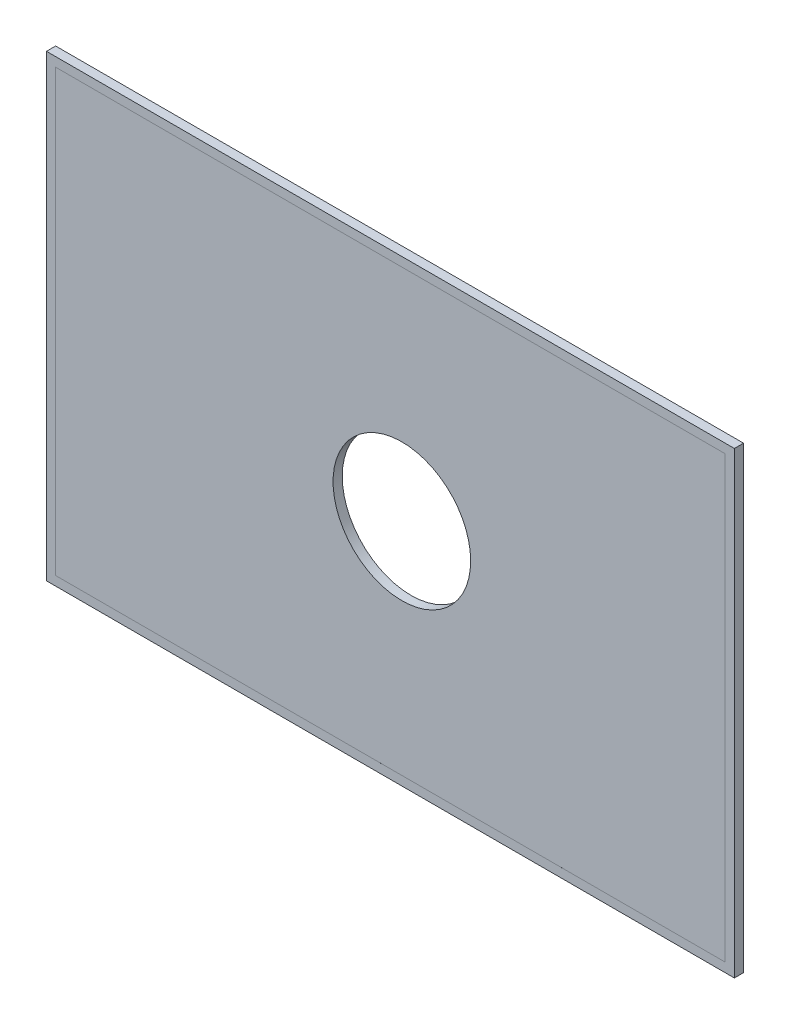
SolidWorks part; units mm, degrees
ref_plane "Plan de face" through (0, 0, 0) normal (0, 0, 1) x (1, 0, 0)
ref_plane "Plan de dessus" through (0, 0, 0) normal (0, 1, 0) x (1, 0, 0)
ref_plane "Plan de droite" through (0, 0, 0) normal (1, 0, 0) x (0, 0, -1)
sketch "Esquisse2" plane through (0, 0, 0) normal (0, 0, 1) x (1, 0, 0)
  line L1 (0, 0) -> (150, 0)
  line L2 (0, 0) -> (0, 100)
  line L3 (0, 100) -> (150, 100)
  line L4 (150, 0) -> (150, 100)
  dimension "D1" = 100
  dimension "D2" = 150
extrude "Boss.-Extru.1" add sketch "Esquisse2" along normal blind 2
sketch "Esquisse3" plane through (0, 0, 2) normal (0, 0, 1) x (1, 0, 0)
  line L0 (0, 100) -> (0, 0) construction
  line L1 (148, 98) -> (2, 98)
  line L2 (148, 98) -> (148, 2)
  line L3 (148, 2) -> (2, 2)
  line L4 (2, 98) -> (2, 2)
  line L5 (150, 100) -> (0, 100) construction
  line L6 (150, 0) -> (150, 100) construction
  line L7 (0, 0) -> (150, 0) construction
  dimension "D1" = 2
  dimension "D2" = 2
  dimension "D3" = 2
  dimension "D4" = 2
extrude "Enlèv. mat.-Extru.1" cut sketch "Esquisse3" against normal blind 0.0001
sketch "Esquisse4" plane through (0, 0, 1.9999) normal (0, 0, 1) x (1, 0, 0)
  line L0 (0, 100) -> (0, 0) construction
  line L1 (150, 100) -> (0, 100) construction
  circle A0 centre (77.5, 50) radius 15
  point P6 (0, 0)
  dimension "D2" = 30
  dimension "D3" = 50
  dimension "D1" = 77.5
extrude "Enlèv. mat.-Extru.2" cut sketch "Esquisse4" against normal blind 2.5 contours A0
